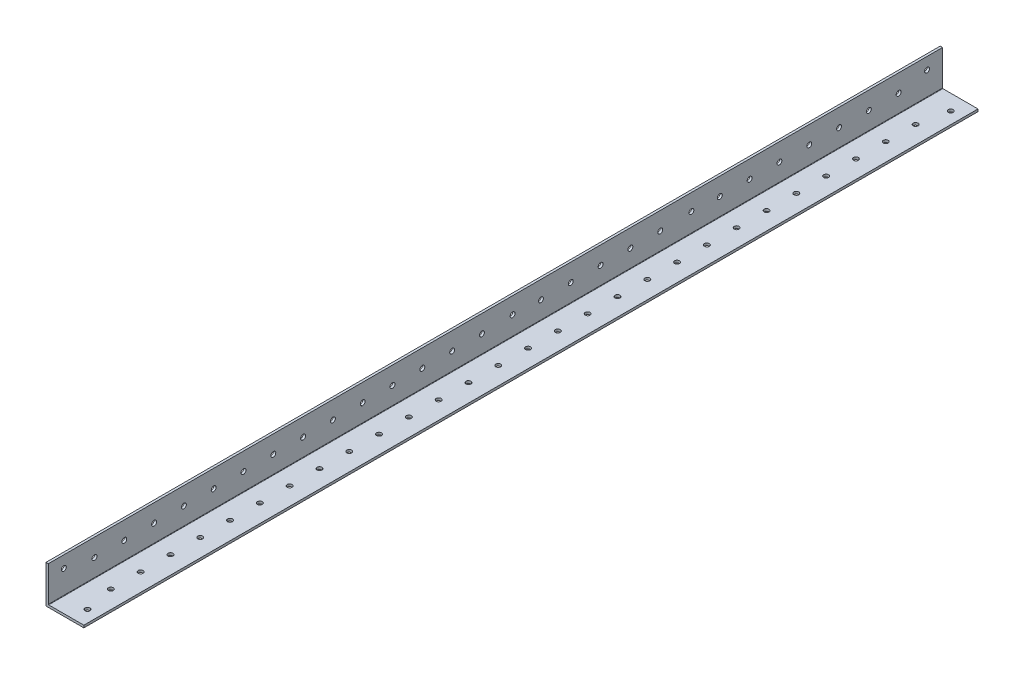
SolidWorks part; units mm, degrees
material "6061 Alloy"
ref_plane "Front Plane" through (0, 0, 0) normal (0, 0, 1) x (1, 0, 0)
ref_plane "Top Plane" through (0, 0, 0) normal (0, 1, 0) x (1, 0, 0)
ref_plane "Right Plane" through (0, 0, 0) normal (1, 0, 0) x (0, 0, -1)
sketch "Sketch1" plane through (0, 0, 0) normal (0, 0, 1) x (1, 0, 0)
  line L0 (0, 25.4) -> (0, 0) construction
  line L1 (0, 0) -> (25.4, 0) construction
  line L2 (25.4, 0) -> (25.4, 1.5875) construction
  line L3 (25.4, 1.5875) -> (1.5875, 1.5875) construction
  line L4 (1.5875, 1.5875) -> (1.5875, 25.4) construction
  line L6 (1.5875, 25.4) -> (0, 25.4) construction
  arc A0 (1.5875, 1.8415) -> (1.8415, 1.5875) centre (1.8415, 1.8415) ccw construction
  point P4 (0, 0)
  dimension "Inside Corner Radius" = 0.254
  dimension "Outside Height" = 25.4
  dimension "Inside Height" = 23.8125
  dimension "Outside Width" = 25.4
  dimension "Inside Width" = 23.8125
  dimension "Wall Thickness" = 1.5875
  dimension "Shape" = 90
sketch "Sketch2" plane through (0, 0, 0) normal (1, 0, 0) x (0, 0, -1)
  line L0 (1219.2, 0) -> (-1219.2, 0) construction
  line L1 (-1219.2, 25.4) -> (-1219.2, 0) construction
  line L2 (1219.2, 25.4) -> (1219.2, 0) construction
  point P0 (-1189.99, 0)
  point P4 (0, 0)
  point P6 (1189.99, 0)
  dimension "D1" = 29.21
  dimension "D2" = 29.21
  dimension "D3" = 25.4
  dimension "Length" = 2438.4
sketch "Sketch3" plane through (0, 0, 0) normal (0, 0, 1) x (1, 0, 0)
  line L0 (1.5875, 25.4) -> (0, 25.4)
  line L1 (0, 25.4) -> (0, 0)
  line L2 (0, 0) -> (25.4, 0)
  line L3 (25.4, 0) -> (25.4, 1.5875)
  line L4 (25.4, 1.5875) -> (1.5875, 1.5875)
  line L5 (1.5875, 1.5875) -> (1.5875, 25.4)
extrude "Boss-Extrude1" add sketch "Sketch3" along normal mid plane 2438.4
fillet "Fillet1" radius 0.254 1 edges at (1.5875, 1.5875, 0)
sketch "Sketch4" plane through (0, 0, 0) normal (-1, 0, 0) x (0, 0, 1)
  line L0 (1219.2, 25.4) -> (1219.2, 0) construction
  line L1 (-1219.2, 0) -> (619.2, 0)
  line L2 (-1219.2, 0) -> (-1219.2, 74.9453)
  line L3 (-1219.2, 74.9453) -> (619.2, 74.9453)
  line L4 (619.2, 0) -> (619.2, 74.9453)
  dimension "D1" = 600
extrude "Cut-Extrude1" cut sketch "Sketch4" against normal blind 60
sketch "Sketch5" plane through (0, 1.5875, 0) normal (0, 1, 0) x (1, 0, 0)
  line L0 (17.4625, -1208.8241) -> (17.4625, -1189.2) construction
  line L1 (13.4937, -649.2) -> (13.4937, -629.5759) construction
  line L3 (1.5875, -1189.2) -> (25.4, -1189.2) construction
  line L4 (1.5875, -1219.2) -> (1.5875, -619.2) construction
  line L5 (25.4, -1219.2) -> (25.4, -619.2) construction
  line L6 (13.4937, -629.5759) -> (17.4625, -629.5759) construction
  line L7 (17.4625, -629.5759) -> (13.4937, -629.5759) construction
  circle A30 centre (17.4625, -629.5759) radius 1.65
  circle A31 centre (17.4625, -1208.8241) radius 1.65
  circle A32 centre (13.4938, -1189.2) radius 1.65
  circle A33 centre (13.4938, -1169.2) radius 1.65
  circle A34 centre (13.4938, -1149.2) radius 1.65
  circle A35 centre (13.4938, -1129.2) radius 1.65
  circle A36 centre (13.4938, -1109.2) radius 1.65
  circle A37 centre (13.4938, -1089.2) radius 1.65
  circle A38 centre (13.4938, -1069.2) radius 1.65
  circle A39 centre (13.4938, -1049.2) radius 1.65
  circle A40 centre (13.4938, -1029.2) radius 1.65
  circle A41 centre (13.4938, -1009.2) radius 1.65
  circle A42 centre (13.4938, -989.2) radius 1.65
  circle A43 centre (13.4938, -969.2) radius 1.65
  circle A44 centre (13.4938, -949.2) radius 1.65
  circle A45 centre (13.4938, -929.2) radius 1.65
  circle A46 centre (13.4938, -909.2) radius 1.65
  circle A47 centre (13.4938, -889.2) radius 1.65
  circle A48 centre (13.4938, -869.2) radius 1.65
  circle A49 centre (13.4938, -849.2) radius 1.65
  circle A50 centre (13.4938, -829.2) radius 1.65
  circle A51 centre (13.4938, -809.2) radius 1.65
  circle A52 centre (13.4938, -789.2) radius 1.65
  circle A53 centre (13.4938, -769.2) radius 1.65
  circle A54 centre (13.4938, -749.2) radius 1.65
  circle A55 centre (13.4938, -729.2) radius 1.65
  circle A56 centre (13.4938, -709.2) radius 1.65
  circle A57 centre (13.4938, -689.2) radius 1.65
  circle A58 centre (13.4938, -669.2) radius 1.65
  circle A59 centre (13.4937, -649.2) radius 1.65
  dimension "D1" = 3.3
  dimension "D2" = 3.3
  dimension "D3" = 28
  dimension "D4" = 20
extrude "Cut-Extrude2" cut sketch "Sketch5" against normal blind 10
sketch "Sketch9" plane through (1.5875, 0, 0) normal (1, 0, 0) x (0, 0, -1)
  line L0 (-648.6348, 1.5875) -> (-648.6348, 25.4) construction
  line L1 (-1219.2, 1.5875) -> (-619.2, 1.5875) construction
  line L2 (-1219.2, 25.4) -> (-619.2, 25.4) construction
  line L3 (-629.5759, 17.4625) -> (-648.6348, 17.4625) construction
  line L4 (-634.3937, -3.175) -> (-630.9937, -3.175) construction
  line L5 (-634.3937, 0) -> (-634.3937, -6.35) construction
  line L6 (-630.9937, -6.35) -> (-630.9937, 0) construction
  line L8 (-632.6938, 209.4245) -> (-632.6938, 9.1639) construction
  line L9 (-631.1938, 209.4245) -> (-634.1938, 209.4245) construction
  line L10 (-888.6348, 13.4937) -> (-907.6938, 13.4937) construction
  line L11 (-632.6938, 9.1639) -> (-787.6938, 9.1639) construction
  line L12 (-1208.8241, 17.463) -> (-1208.8241, 3.8191) construction
  line L13 (-1215.3265, 3.8191) -> (-1204.9125, 3.8191) construction
  line L14 (-787.6938, 9.1639) -> (-787.6938, 14.2875) construction
  line L15 (-648.6348, 189.6807) -> (-629.5759, 189.6807) construction
  line L16 (-629.5759, 189.6807) -> (-629.5759, 185.712) construction
  line L17 (-768.6348, 13.4937) -> (-787.6938, 13.4937) construction
  line L18 (-787.6938, 13.4937) -> (-787.6938, 14.2875) construction
  line L19 (-907.6938, 13.4937) -> (-907.6938, 14.2875) construction
  line L20 (-787.6938, 13.4937) -> (-787.6938, 14.2875) construction
  line L21 (-1188.2589, 25.4) -> (-1188.2589, 1.5875) construction
  line L22 (-907.6938, 13.4937) -> (-907.6938, 14.2875) construction
  line L23 (-1188.2589, 189.6808) -> (-1188.2589, 177.7745) construction
  line L24 (-1219.2, 177.7745) -> (-619.2, 177.7745) construction
  circle A0 centre (-629.5759, 17.4625) radius 1.65
  circle A3 centre (-1208.8241, 17.463) radius 1.65
  circle A16 centre (-1188.2589, 13.4937) radius 1.65
  circle A32 centre (-1168.2589, 13.4937) radius 1.65
  circle A33 centre (-1148.2589, 13.4937) radius 1.65
  circle A34 centre (-1128.2589, 13.4937) radius 1.65
  circle A35 centre (-1108.2589, 13.4937) radius 1.65
  circle A36 centre (-1088.2589, 13.4937) radius 1.65
  circle A37 centre (-1068.2589, 13.4937) radius 1.65
  circle A38 centre (-1048.2589, 13.4937) radius 1.65
  circle A39 centre (-1028.2589, 13.4937) radius 1.65
  circle A40 centre (-1008.2589, 13.4937) radius 1.65
  circle A41 centre (-988.2589, 13.4937) radius 1.65
  circle A42 centre (-968.2589, 13.4937) radius 1.65
  circle A43 centre (-948.2589, 13.4937) radius 1.65
  circle A44 centre (-928.2589, 13.4937) radius 1.65
  circle A73 centre (-787.6938, 14.2875) radius 1.65
  circle A74 centre (-907.6938, 14.2875) radius 1.65
  circle A75 centre (-648.6348, 13.4937) radius 1.65
  circle A76 centre (-668.6348, 13.4937) radius 1.65
  circle A77 centre (-688.6348, 13.4937) radius 1.65
  circle A78 centre (-708.6348, 13.4937) radius 1.65
  circle A79 centre (-728.6348, 13.4937) radius 1.65
  circle A80 centre (-748.6348, 13.4937) radius 1.65
  circle A81 centre (-768.6348, 13.4937) radius 1.65
  circle A87 centre (-808.6348, 13.4937) radius 1.65
  circle A89 centre (-828.6348, 13.4937) radius 1.65
  circle A90 centre (-848.6348, 13.4937) radius 1.65
  circle A91 centre (-868.6348, 13.4937) radius 1.65
  circle A92 centre (-888.6348, 13.4937) radius 1.65
  dimension "D1" = 12.7
  dimension "D3" = 3.3
  dimension "D4" = 155
  dimension "D5" = 275
  dimension "D6" = 3.3
  dimension "D8" = 40
  dimension "D2" = 3.3
  dimension "D10" = 3.3
  dimension "D9" = 19.0589
  dimension "D11" = 20
  dimension "D7" = 7
extrude "Cut-Extrude6" cut sketch "Sketch9" against normal blind 60
equation "\"D1@Boss-Extrude1\"=\"Length@Sketch2\""
equation "\"D1@Sketch2\" = \"Outside Width@Sketch1\" * 1.15"
equation "\"D2@Sketch2\"=\"D1@Sketch2\""
equation "\"D1@Fillet1\"=\"Inside Corner Radius@Sketch1\""
equation "\"D3@Sketch2\"=\"Outside Height@Sketch1\""
